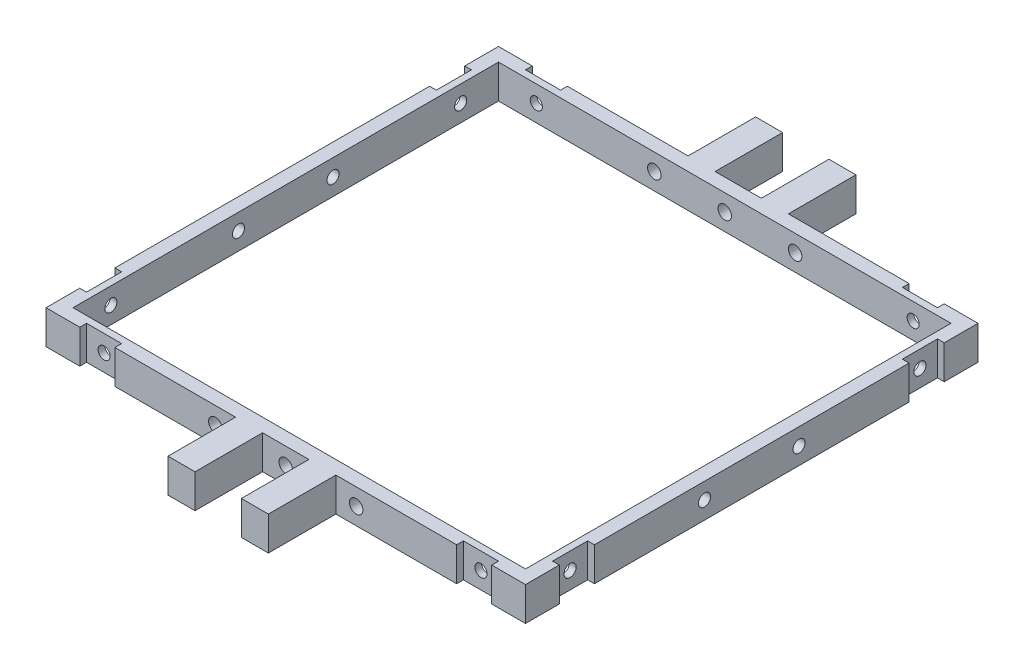
SolidWorks part; units mm, degrees
ref_plane "Front Plane" through (0, 0, 0) normal (0, 0, 1) x (1, 0, 0)
ref_plane "Top Plane" through (0, 0, 0) normal (0, 1, 0) x (1, 0, 0)
ref_plane "Right Plane" through (0, 0, 0) normal (1, 0, 0) x (0, 0, -1)
sketch "Sketch1" plane through (0, 0, 0) normal (0, 1, 0) x (1, 0, 0)
  line L1 (-35.5, 33.5) -> (35.5, 33.5)
  line L2 (-35.5, 33.5) -> (-35.5, -33.5)
  line L3 (-35.5, -33.5) -> (35.5, -33.5)
  line L4 (35.5, 33.5) -> (35.5, -33.5)
  line L5 (-35.5, 33.5) -> (35.5, -33.5) construction
  line L6 (-35.5, -33.5) -> (35.5, 33.5) construction
  line L7 (-33.5, 31.5) -> (33.5, 31.5)
  line L8 (-33.5, 31.5) -> (-33.5, -31.5)
  line L9 (-33.5, -31.5) -> (33.5, -31.5)
  line L10 (33.5, 31.5) -> (33.5, -31.5)
  line L11 (-33.5, 31.5) -> (33.5, -31.5) construction
  line L12 (-33.5, -31.5) -> (33.5, 31.5) construction
  point P0 (0, 0)
  point P6 (0, 0)
  dimension "D1" = 67
  dimension "D2" = 71
  dimension "D3" = 2
  dimension "D4" = 2
extrude "Boss-Extrude1" add sketch "Sketch1" along normal blind 5
sketch "Sketch2" plane through (35.5, 0, 0) normal (1, 0, 0) x (0, 0, -1)
  line L1 (-33.5, 5) -> (33.5, 5) construction
  circle A0 centre (-6.9997, 2.5914) radius 0.9
  circle A1 centre (7, 2.5) radius 0.9
  dimension "D1" = 14
  dimension "D2" = 2.5
  dimension "D3" = 7
  dimension "D4" = 1.8
  dimension "D5" = 1.8
  dimension "D6" = 6.9997
extrude "Cut-Extrude1" cut sketch "Sketch2" against normal blind 121
sketch "Sketch3" plane through (0, 0, 33.5) normal (0, 0, 1) x (1, 0, 0)
  line L0 (-35.5, 5) -> (35.5, 5) construction
  circle A0 centre (0, 2.5) radius 1
  dimension "D1" = 2
  dimension "D2" = 2.5
  dimension "D3" = 0
extrude "Cut-Extrude2" cut sketch "Sketch3" against normal blind 90
sketch "Sketch4" plane through (0, 0, 33.5) normal (0, 0, 1) x (1, 0, 0)
  line L0 (-35.5, 0) -> (35.5, 0) construction
  line L1 (3.425, 5) -> (7.425, 5)
  line L2 (3.425, 5) -> (3.425, 0)
  line L3 (3.425, 0) -> (7.425, 0)
  line L4 (7.425, 5) -> (7.425, 0)
  line L7 (-3.4289, 5) -> (-7.4289, 5)
  line L8 (-3.4289, 5) -> (-3.4289, 0)
  line L9 (-3.4289, 0) -> (-7.4289, 0)
  line L10 (-7.4289, 5) -> (-7.4289, 0)
  dimension "D1" = 4
  dimension "D2" = 4
  dimension "D3" = 5
  dimension "D4" = 5
  dimension "D5" = 6.8539
  dimension "D6" = 0
  dimension "D7" = 0
  dimension "D8" = 3.425
extrude "Boss-Extrude2" add sketch "Sketch4" along normal blind 10
ref_plane "Plane1" through (0, 0, 0) normal (0, 0, 1) x (1, 0, 0)
mirror "Mirror1" about plane through (0, 0, 0) normal (0, 0, 1) of "Boss-Extrude2"
sketch "Sketch5" plane through (0, 0, 33.5) normal (0, 0, 1) x (1, 0, 0)
  line L0 (-7.4289, 5) -> (-7.4289, 0) construction
  line L1 (7.425, 0) -> (7.425, 5) construction
  line L2 (7.425, 5) -> (35.5, 5) construction
  line L3 (-35.5, 5) -> (-7.4289, 5) construction
  circle A0 centre (-10.4289, 2.5) radius 1
  circle A1 centre (10.425, 2.5) radius 1
  dimension "D1" = 3
  dimension "D2" = 3
  dimension "D3" = 2.5
  dimension "D4" = 2.5
  dimension "D5" = 2
  dimension "D6" = 2
extrude "Cut-Extrude3" cut sketch "Sketch5" against normal blind 109
sketch "Sketch9" plane through (0, 0, 33.5) normal (0, 0, 1) x (1, 0, 0)
  line L0 (-35.5, 5) -> (-7.4289, 5) construction
  line L1 (-30.5, 5) -> (-25.3, 5)
  line L2 (-30.5, 5) -> (-30.5, 0)
  line L3 (-30.5, 0) -> (-25.3, 0)
  line L4 (-25.3, 5) -> (-25.3, 0)
  line L5 (-35.5, 0) -> (-7.4289, 0) construction
  line L6 (7.425, 0) -> (35.5, 0) construction
  line L7 (30.5, 5) -> (25.3, 5)
  line L8 (30.5, 5) -> (30.5, 0)
  line L9 (30.5, 0) -> (25.3, 0)
  line L10 (25.3, 5) -> (25.3, 0)
  line L11 (-35.5, 5) -> (-35.5, 0) construction
  line L12 (35.5, 5) -> (35.5, 0) construction
  dimension "D1" = 5.2
  dimension "D2" = 5
  dimension "D3" = 5
  dimension "D4" = 5.2
extrude "Cut-Extrude6" cut sketch "Sketch9" against normal blind 1
sketch "Sketch10" plane through (35.5, 0, 0) normal (1, 0, 0) x (0, 0, -1)
  line L0 (-33.5, 5) -> (33.5, 5) construction
  line L1 (-28.5, 5) -> (-23.3, 5)
  line L2 (-28.5, 5) -> (-28.5, 0)
  line L3 (-28.5, 0) -> (-23.3, 0)
  line L4 (-23.3, 5) -> (-23.3, 0)
  line L5 (-33.5, 0) -> (33.5, 0) construction
  line L6 (33.5, 5) -> (33.5, 0) construction
  line L7 (28.5, 5) -> (23.3, 5)
  line L8 (28.5, 5) -> (28.5, 0)
  line L9 (28.5, 0) -> (23.3, 0)
  line L10 (23.3, 5) -> (23.3, 0)
  line L11 (-33.5, 5) -> (-33.5, 0) construction
  dimension "D1" = 5.2
  dimension "D2" = 5.2
  dimension "D3" = 5
  dimension "D4" = 5
extrude "Cut-Extrude7" cut sketch "Sketch10" against normal blind 1
ref_plane "Plane2" through (0, 0, 0) normal (1, 0, 0) x (0, 0, -1)
mirror "Mirror2" about plane through (0, 0, 0) normal (1, 0, 0) of "Cut-Extrude7"
mirror "Mirror3" about plane through (0, 0, 0) normal (0, 0, 1) of "Cut-Extrude6"
sketch "Sketch11" plane through (34.5, 0, 0) normal (1, 0, 0) x (0, 0, -1)
  circle A0 centre (25.9, 2.5) radius 0.9
  circle A1 centre (-25.9, 2.5) radius 0.9
  dimension "D1" = 1.8
  dimension "D2" = 1.8
extrude "Cut-Extrude8" cut sketch "Sketch11" against normal blind 81
sketch "Sketch12" plane through (0, 0, 32.5) normal (0, 0, 1) x (1, 0, 0)
  circle A0 centre (27.9, 2.5) radius 0.9
  circle A1 centre (-27.9, 2.5) radius 0.9
  dimension "D1" = 1.8
  dimension "D2" = 1.8
extrude "Cut-Extrude9" cut sketch "Sketch12" against normal blind 81
